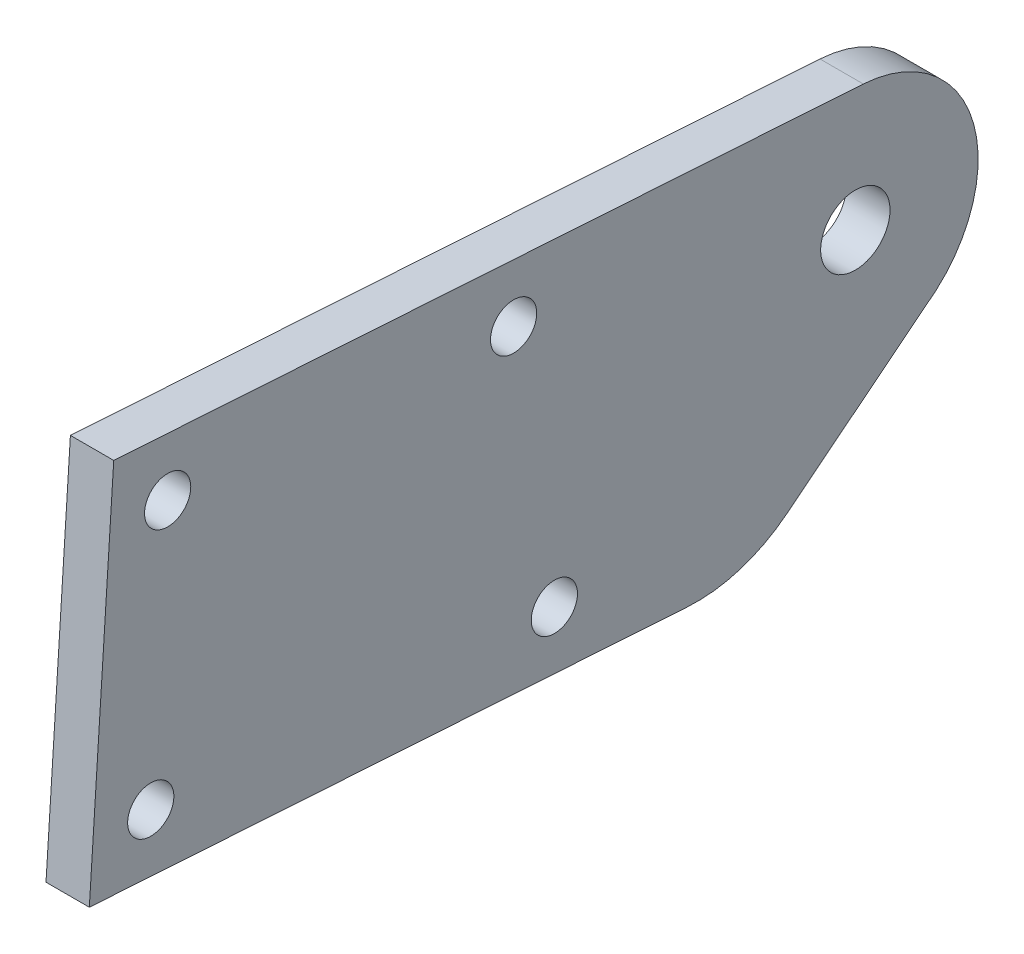
SolidWorks part; units mm, degrees
ref_plane "前视基准面" through (0, 0, 0) normal (0, 0, 1) x (1, 0, 0)
ref_plane "上视基准面" through (0, 0, 0) normal (0, 1, 0) x (1, 0, 0)
ref_plane "右视基准面" through (0, 0, 0) normal (1, 0, 0) x (0, 0, -1)
sketch "草图1" plane through (0, 0, 0) normal (1, 0, 0) x (0, 0, -1)
  line L47 (-52.9884, -14.1911) -> (-11.5761, -16.8876)
  line L48 (-4.6974, -14.7317) -> (5.6324, -6.5068)
  line L49 (-51.2991, 11.7539) -> (-52.9884, -14.1911)
  line L50 (-51.2991, 11.7539) -> (0.5911, 8.3753)
  circle A0 centre (0.0388, -0.1068) radius 2.4
  circle A166 centre (-47.5674, 7.5025) radius 1.6
  arc A169 (5.6324, -6.5068) -> (0.5911, 8.3753) centre (0.0388, -0.1068) ccw
  circle A170 centre (-20.7961, -12.2788) radius 1.6
  circle A171 centre (-23.6181, 5.9431) radius 1.6
  circle A175 centre (-48.7369, -10.4595) radius 1.6
  arc A176 (-11.5761, -16.8876) -> (-4.6974, -14.7317) centre (-10.9263, -6.9087) ccw
  point P0 (-150, 0)
  point P1 (135, 0)
  point P9 (-344.9533, 138.7825)
  point P10 (187.1329, 101.1747)
  point P11 (165.9429, -19)
  point P12 (-156.9154, -19)
  dimension "D7" = 4
  dimension "D8" = 22
  dimension "D9" = 52
  dimension "D10" = 8.5
  dimension "D4" = 4
  dimension "D11" = 52
  dimension "D12" = 41.5
  dimension "D13" = 26
  dimension "D14" = 90
  dimension "D15" = 4.8
  dimension "D6" = 28
  dimension "D5" = 4
  dimension "D2" = 18
  dimension "D1" = 24
  dimension "D3" = 4
extrude "凸台-拉伸1" add sketch "草图1" along normal blind 3
